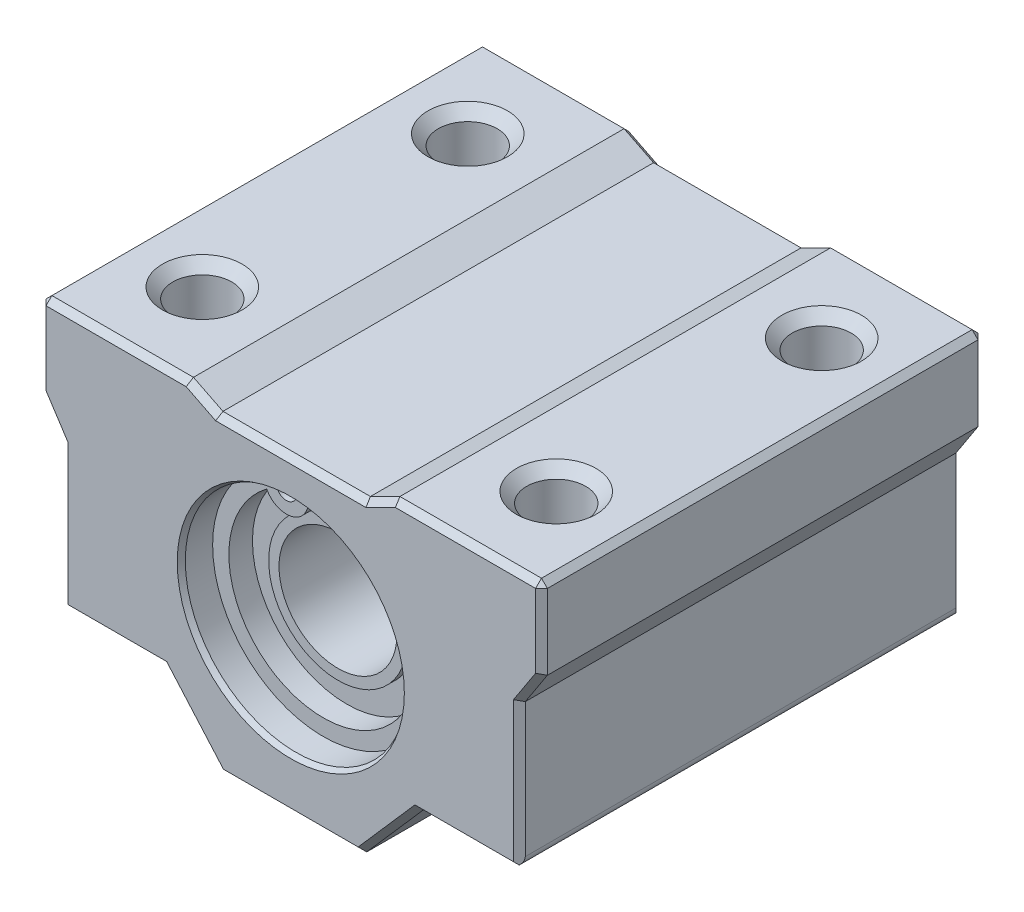
SolidWorks part; units mm, degrees
material "1060 Alloy"
ref_plane "Front Plane" through (0, 0, 0) normal (0, 0, 1) x (1, 0, 0)
ref_plane "Top Plane" through (0, 0, 0) normal (0, 1, 0) x (1, 0, 0)
ref_plane "Right Plane" through (0, 0, 0) normal (1, 0, 0) x (0, 0, -1)
sketch "Sketch1" plane through (0, 0, 0) normal (0, 0, 1) x (1, 0, 0)
  line L0 (0, 0) -> (0, -120.6263) construction
  line L1 (-5, -1) -> (5, -1)
  line L2 (5, -1) -> (7, 0)
  line L3 (7, 0) -> (17, 0)
  line L4 (17, 0) -> (17, -5.5)
  line L5 (17, -5.5) -> (15.5, -7.8)
  line L6 (15.5, -7.8) -> (15.5, -17.6)
  line L7 (15.5, -17.6) -> (8.6, -17.6)
  line L8 (8.6, -17.6) -> (4.75, -22)
  line L9 (4.75, -22) -> (-4.75, -22)
  line L10 (-15.5, -7.8) -> (-15.5, -17.6)
  line L11 (-17, -5.5) -> (-15.5, -7.8)
  line L12 (-17, 0) -> (-17, -5.5)
  line L13 (-7, 0) -> (-17, 0)
  line L14 (-5, -1) -> (-7, 0)
  line L15 (-15.5, -17.6) -> (-8.6, -17.6)
  line L16 (-8.6, -17.6) -> (-4.75, -22)
  circle A0 centre (0, -11) radius 7.5
  point P19 (0, -1)
  point P21 (0, -22)
  dimension "D4" = 15
  dimension "D1" = 5.5
  dimension "D2" = 1
  dimension "D3" = 1.5
  dimension "D5" = 34
  dimension "D6" = 22
  dimension "D7" = 7.8
  dimension "D8" = 2
  dimension "D9" = 17.6
  dimension "D10" = 11
  dimension "D11" = 10
  dimension "D12" = 9.5
  dimension "D13" = 17.2
extrude "Boss-Extrude1" add sketch "Sketch1" along normal mid plane 30
sketch "Sketch2" plane through (0, 0, 0) normal (1, 0, 0) x (0, 0, -1)
  line L0 (-30.2753, -11) -> (15, -11) construction
  line L1 (15, -18.5) -> (15, -3.5) construction
  line L2 (15, -18.5) -> (15, -3.5) construction
  line L3 (0, 0) -> (0, -32.2949) construction
  line L4 (-12, -3.5) -> (12, -3.5)
  line L5 (12, -3.5) -> (12, -4.6)
  line L6 (12, -4.6) -> (11.2, -4.6)
  line L7 (11.2, -4.6) -> (11.2, -6.3)
  line L8 (11.2, -6.3) -> (11.8, -6.3)
  line L9 (11.8, -6.3) -> (11.8, -7)
  line L10 (11.8, -7) -> (-11.8, -7)
  line L11 (-11.8, -6.3) -> (-11.8, -7)
  line L12 (-11.2, -6.3) -> (-11.8, -6.3)
  line L13 (-11.2, -4.6) -> (-11.2, -6.3)
  line L14 (-12, -4.6) -> (-11.2, -4.6)
  line L15 (-12, -3.5) -> (-12, -4.6)
  line L16 (11.8, -15) -> (-11.8, -15) construction
  line L17 (-12, -18.5) -> (12, -18.5) construction
  point P16 (0, -7)
  point P21 (0, -3.5)
  dimension "D1" = 1.1
  dimension "D2" = 0.7
  dimension "D3" = 15
  dimension "D4" = 8
  dimension "D5" = 24
  dimension "D6" = 0.8
  dimension "D7" = 0.6
revolve "Revolve1" add sketch "Sketch2" angle 360 about L0
sketch "Sketch3" plane through (0, 0, 12) normal (0, 0, 1) x (1, 0, 0)
  line L0 (0, 4.2304) -> (0, -35.7092) construction
  circle A0 centre (2.5, -5.1858) radius 0.7
  circle A1 centre (0, -11) radius 6.4 construction
  arc A2 (2, -3.7716) -> (3.8326, -5.8744) centre (2.5, -5.1858) ccw
  arc A3 (2, -3.7716) -> (-2, -3.7716) centre (0, -11) cw
  arc A4 (3.8326, -5.8744) -> (-3.8326, -5.8744) centre (0, -11) cw
  circle A5 centre (-2.5, -5.1858) radius 0.7
  arc A6 (-2, -3.7716) -> (-3.8326, -5.8744) centre (-2.5, -5.1858) cw
  circle A7 centre (0, -11) radius 7.5 construction
  circle A8 centre (0, -11) radius 7.5 construction
  dimension "D1" = 1.5
  dimension "D3" = 2.5
  dimension "D2" = 1.4
  dimension "D4" = 2
extrude "Boss-Extrude2" add sketch "Sketch3" along normal blind 0.8
mirror "simetria" about plane through (0, 0, 0) normal (0, 0, 1) of "Boss-Extrude2"
chamfer "Chaflàn0" distance 0.2 angle 60 2 edges at (7.5, -11, -15) (7.5, -11, 15)
sketch "Croquis1" plane through (0, 0, 0) normal (0, 1, 0) x (1, 0, 0)
  line L0 (0, 0) -> (-17, 0) construction
  line L1 (-17, -15) -> (-17, 15) construction
  line L2 (-12, 15) -> (-12, -15) construction
  line L3 (-7, 15) -> (-17, 15) construction
  line L4 (-7, -15) -> (-17, -15) construction
  line L5 (12, 15) -> (12, -15) construction
  line L6 (17, 15) -> (7, 15) construction
  line L7 (17, -15) -> (7, -15) construction
  circle A0 centre (-12, 9) radius 2
  circle A1 centre (12, 9) radius 2
  circle A2 centre (-12, -9) radius 2
  circle A3 centre (12, -9) radius 2
  dimension "D1" = 4
  dimension "D2" = 4
  dimension "D3" = 4
  dimension "D4" = 4
  dimension "D5" = 18
  dimension "D6" = 9
  dimension "D7" = 9
  dimension "D8" = 9
extrude "Cortar-Extruir1" cut sketch "Croquis1" against normal blind 20
chamfer "Chaflán1" distance 0.7 angle 45 8 edges at (-14, -17.6, 9) (-14, -17.6, -9) (10, -17.6, 9) (10, -17.6, -9) (10, 0, 9) (-14, 0, 9) (10, 0, -9) (-14, 0, -9)
chamfer "Chaflán2" distance 0.4 angle 45 34 edges at (12, 0, 15) (17, -2.75, 15) (16.25, -6.65, 15) (15.5, -12.7, 15) (12.05, -17.6, 15) (6.675, -19.8, 15) (0, -22, 15) (-6.675, -19.8, 15) (-12.05, -17.6, 15) (-15.5, -12.7, 15) (-16.25, -6.65, 15) (-17, -2.75, 15) (-12, 0, 15) (-6, -0.5, 15) (0, -1, 15) (6, -0.5, 15) (0, -1, -15) (-6, -0.5, -15) (-12, 0, -15) (-17, -2.75, -15) (-16.25, -6.65, -15) (-15.5, -12.7, -15) (-12.05, -17.6, -15) (-6.675, -19.8, -15) (0, -22, -15) (6.675, -19.8, -15) (12.05, -17.6, -15) (15.5, -12.7, -15) (16.25, -6.65, -15) (17, -2.75, -15) (12, 0, -15) (6, -0.5, -15) (17, 0, 0) (-17, 0, 0)
fillet "Redondeo1" radius 0.7 2 edges at (15.5, -17.6, 0) (-15.5, -17.6, 0)
